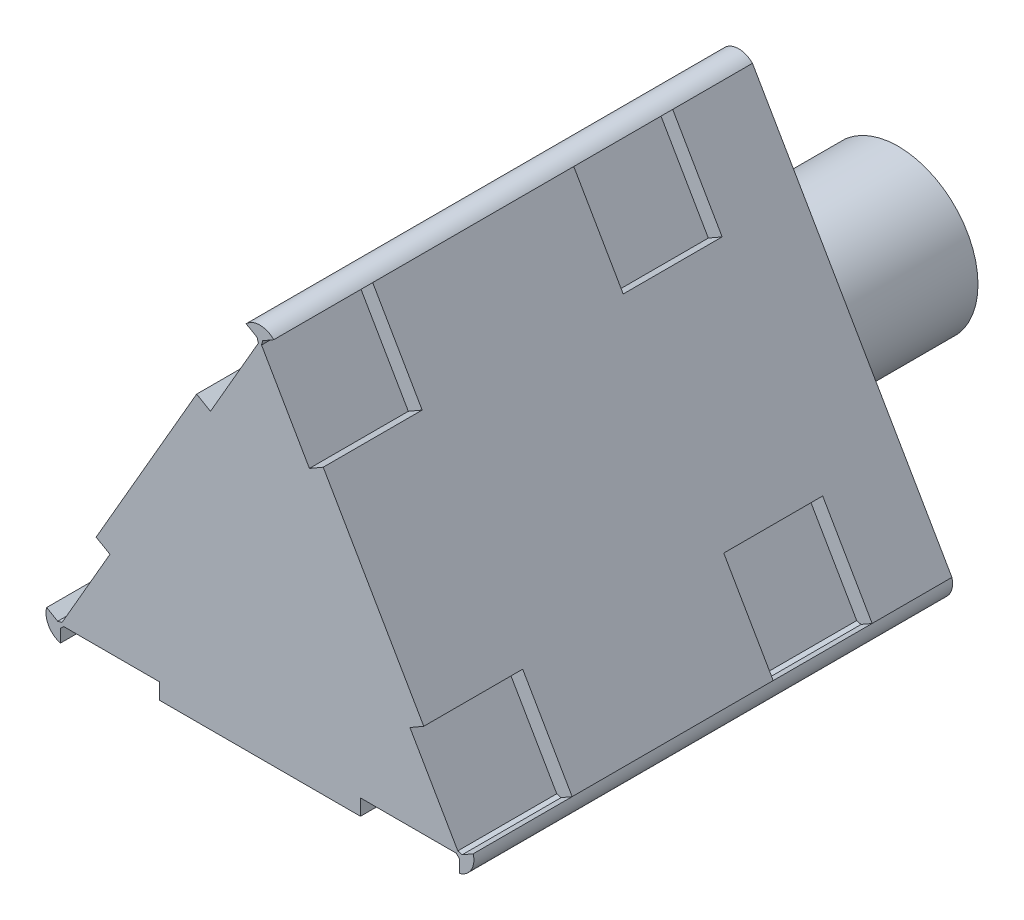
SolidWorks part; units mm, degrees
ref_plane "正面" through (0, 0, 0) normal (0, 0, 1) x (1, 0, 0)
ref_plane "平面" through (0, 0, 0) normal (0, 1, 0) x (1, 0, 0)
ref_plane "右側面" through (0, 0, 0) normal (1, 0, 0) x (0, 0, -1)
sketch "ｽｹｯﾁ1" plane through (0, 0, 0) normal (0, 0, 1) x (1, 0, 0)
  line L0 (0, 21.6506) -> (-12.5, 0)
  line L1 (-12.5, 0) -> (12.5, 0)
  line L2 (12.5, 0) -> (0, 21.6506)
  dimension "D1" = 25
extrude "ﾎﾞｽ - 押し出し1" add sketch "ｽｹｯﾁ1" along normal blind 30
sketch "ｽｹｯﾁ2" plane through (-9.375, 5.4127, 0) normal (-0.866, 0.5, 0) x (0, 0, 1)
  line L0 (30, -6.25) -> (0, -6.25) construction
  line L1 (30, -6.25) -> (23.8, -6.25)
  line L2 (30, -6.25) -> (30, -0.05)
  line L3 (30, -0.05) -> (23.8, -0.05)
  line L4 (23.8, -6.25) -> (23.8, -0.05)
  line L5 (30, 18.75) -> (23.8, 18.75)
  line L6 (30, 18.75) -> (30, 12.55)
  line L7 (30, 12.55) -> (23.8, 12.55)
  line L8 (23.8, 18.75) -> (23.8, 12.55)
  line L9 (11.2, -6.25) -> (5, -6.25)
  line L10 (11.2, -6.25) -> (11.2, -0.05)
  line L11 (11.2, -0.05) -> (5, -0.05)
  line L12 (5, -6.25) -> (5, -0.05)
  line L13 (30, 18.75) -> (0, 18.75) construction
  line L14 (11.2, 18.75) -> (5, 18.75)
  line L15 (11.2, 18.75) -> (11.2, 12.55)
  line L16 (11.2, 12.55) -> (5, 12.55)
  line L17 (5, 18.75) -> (5, 12.55)
  dimension "D1" = 6.2
  dimension "D2" = 6.2
  dimension "D3" = 6.2
  dimension "D4" = 6.2
  dimension "D5" = 6.2
  dimension "D6" = 6.2
  dimension "D7" = 6.2
  dimension "D8" = 6.2
  dimension "D9" = 25
sketch "ｽｹｯﾁ15" plane through (0, 0, 0) normal (0, -1, 0) x (1, 0, 0)
  line L0 (12.5, 30) -> (12.5, 0) construction
  line L1 (-12.5, 30) -> (-6.3, 30)
  line L2 (-12.5, 30) -> (-12.5, 23.8)
  line L3 (-12.5, 23.8) -> (-6.3, 23.8)
  line L4 (-6.3, 30) -> (-6.3, 23.8)
  line L5 (12.5, 30) -> (6.3, 30)
  line L6 (12.5, 30) -> (12.5, 23.8)
  line L7 (12.5, 23.8) -> (6.3, 23.8)
  line L8 (6.3, 30) -> (6.3, 23.8)
  line L9 (12.5, 5) -> (6.3, 5)
  line L10 (12.5, 5) -> (12.5, 11.2)
  line L11 (12.5, 11.2) -> (6.3, 11.2)
  line L12 (6.3, 5) -> (6.3, 11.2)
  line L13 (-12.5, 30) -> (-12.5, 0) construction
  line L14 (-12.5, 5) -> (-6.3, 5)
  line L15 (-12.5, 5) -> (-12.5, 11.2)
  line L16 (-12.5, 11.2) -> (-6.3, 11.2)
  line L17 (-6.3, 5) -> (-6.3, 11.2)
  dimension "D1" = 6.2
  dimension "D2" = 6.2
  dimension "D3" = 6.2
  dimension "D4" = 6.2
  dimension "D5" = 6.2
  dimension "D6" = 6.2
  dimension "D7" = 6.2
  dimension "D8" = 6.2
  dimension "D9" = 25
sketch "ｽｹｯﾁ20" plane through (9.375, 5.4127, 0) normal (0.866, 0.5, 0) x (0, 0, -1)
  line L0 (-30, -6.25) -> (0, -6.25) construction
  line L1 (-30, -6.25) -> (-23.8, -6.25)
  line L2 (-30, -6.25) -> (-30, -0.05)
  line L3 (-30, -0.05) -> (-23.8, -0.05)
  line L4 (-23.8, -6.25) -> (-23.8, -0.05)
  line L5 (-30, 18.75) -> (-23.8, 18.75)
  line L6 (-30, 18.75) -> (-30, 12.55)
  line L7 (-30, 12.55) -> (-23.8, 12.55)
  line L8 (-23.8, 18.75) -> (-23.8, 12.55)
  line L9 (-5, -6.25) -> (-11.2, -6.25)
  line L10 (-5, -6.25) -> (-5, -0.05)
  line L11 (-5, -0.05) -> (-11.2, -0.05)
  line L12 (-11.2, -6.25) -> (-11.2, -0.05)
  line L13 (-30, 18.75) -> (0, 18.75) construction
  line L14 (-5, 18.75) -> (-11.2, 18.75)
  line L15 (-5, 18.75) -> (-5, 12.55)
  line L16 (-5, 12.55) -> (-11.2, 12.55)
  line L17 (-11.2, 18.75) -> (-11.2, 12.55)
  dimension "D1" = 6.2
  dimension "D2" = 6.2
  dimension "D3" = 6.2
  dimension "D4" = 6.2
  dimension "D5" = 6.2
  dimension "D6" = 6.2
  dimension "D7" = 6.2
  dimension "D8" = 6.2
  dimension "D9" = 25
sketch "ｽｹｯﾁ11" plane through (0, 0, 0) normal (0, 0, -1) x (-1, 0, 0)
  line L0 (0, 21.6506) -> (12.5, 0)
  line L1 (0, 21.6506) -> (0.866, 22.1506) construction
  line L2 (-0.866, 22.1506) -> (0, 21.6506) construction
  line L3 (0.866, 22.1506) -> (13.366, 0.5)
  line L4 (12.5, 0) -> (-12.5, 0)
  line L5 (-13.366, 0.5) -> (-12.5, 0) construction
  line L6 (-12.5, 0) -> (-12.5, -1) construction
  line L7 (12.5, -1) -> (-12.5, -1)
  line L8 (0, 21.6506) -> (-12.5, 0)
  line L9 (12.5, 0) -> (12.5, -1) construction
  line L10 (12.5, 0) -> (13.366, 0.5) construction
  line L11 (-0.866, 22.1506) -> (-13.366, 0.5)
  arc A0 (-0.866, 22.1506) -> (0.866, 22.1506) centre (0, 21.2846) cw
  arc A1 (13.366, 0.5) -> (12.5, -1) centre (12.183, 0.183) cw
  arc A2 (-12.5, -1) -> (-13.366, 0.5) centre (-12.183, 0.183) cw
  dimension "D1" = 25
  dimension "D2" = 1
  dimension "D3" = 25
  dimension "D4" = 1
  dimension "D5" = 25
  dimension "D6" = 1
extrude "ﾎﾞｽ - 押し出し8" add sketch "ｽｹｯﾁ11" against normal through all
extrude "ｶｯﾄ - 押し出し5" cut sketch "ｽｹｯﾁ2" along normal blind 1
sketch "ｽｹｯﾁ16" plane through (0, 0, 23.8) normal (0, 0, 1) x (1, 0, 0)
  line L0 (-12.4, 0.1732) -> (-12.6732, 0.1)
  line L1 (-9.4, 5.3694) -> (-12.5, 0) construction
  line L3 (-12.6732, 0.1) -> (-12.5, 0)
  line L4 (-12.5, 0) -> (-12.4, 0.1732)
  line L7 (-13.366, 0.5) -> (-12.5, 0) construction
  dimension "D1" = 0.2
  dimension "D2" = 0.2
extrude "ﾎﾞｽ - 押し出し9" add sketch "ｽｹｯﾁ16" along normal through all and the other way through all
extrude "ｶｯﾄ - 押し出し10" cut sketch "ｽｹｯﾁ15" along normal blind 1
sketch "ｽｹｯﾁ18" plane through (0, 0, 23.8) normal (0, 0, 1) x (1, 0, 0)
  line L0 (-0.1732, 21.7506) -> (0, 21.6506)
  line L1 (-0.866, 22.1506) -> (0, 21.6506) construction
  line L2 (0, 21.6506) -> (-0.1, 21.4774)
  line L3 (0, 21.6506) -> (-3.1, 16.2813) construction
  line L4 (-0.1, 21.4774) -> (-0.1732, 21.7506)
  dimension "D1" = 0.2
  dimension "D2" = 0.2
extrude "ﾎﾞｽ - 押し出し10" add sketch "ｽｹｯﾁ18" against normal through all and the other way through all
sketch "ｽｹｯﾁ19" plane through (0, 0, 23.8) normal (0, 0, 1) x (1, 0, 0)
  line L0 (12.5, 0) -> (12.3, 0)
  line L1 (6.3, 0) -> (12.5, 0) construction
  line L2 (12.3, 0) -> (12.5, -0.2)
  line L3 (12.5, -1) -> (12.5, 0) construction
  line L4 (12.5, -0.2) -> (12.5, 0)
  dimension "D1" = 0.2
  dimension "D2" = 0.2
extrude "ﾎﾞｽ - 押し出し11" add sketch "ｽｹｯﾁ19" against normal through all and the other way through all
extrude "ｶｯﾄ - 押し出し11" cut sketch "ｽｹｯﾁ20" along normal blind 1
sketch "ｽｹｯﾁ21" plane through (0, 0, 23.8) normal (0, 0, 1) x (1, 0, 0)
  line L0 (0, 21.6506) -> (0.1, 21.4774)
  line L1 (3.1, 16.2813) -> (0, 21.6506) construction
  line L2 (0.1, 21.4774) -> (0.1732, 21.7506)
  line L3 (0.866, 22.1506) -> (0, 21.6506) construction
  line L4 (0.1732, 21.7506) -> (0, 21.6506)
  dimension "D1" = 0.2
  dimension "D2" = 0.2
extrude "ﾎﾞｽ - 押し出し12" add sketch "ｽｹｯﾁ21" along normal through all and the other way through all
sketch "ｽｹｯﾁ23" plane through (0, 0, 23.8) normal (0, 0, 1) x (1, 0, 0)
  line L0 (12.5, 0) -> (12.6732, 0.1)
  line L1 (12.6732, 0.1) -> (12.4, 0.1732)
  line L2 (12.5, 0) -> (9.4, 5.3694) construction
  line L3 (12.4, 0.1732) -> (12.5, 0)
  dimension "D1" = 0.2
  dimension "D2" = 0.2
extrude "ﾎﾞｽ - 押し出し13" add sketch "ｽｹｯﾁ23" along normal through all and the other way through all
sketch "ｽｹｯﾁ24" plane through (0, 0, 23.8) normal (0, 0, 1) x (1, 0, 0)
  line L0 (-12.5, 0) -> (-12.3, 0)
  line L1 (-12.5, 0) -> (-6.3, 0) construction
  line L2 (-12.3, 0) -> (-12.5, -0.2)
  line L3 (-12.5, -1) -> (-12.5, 0) construction
  line L4 (-12.5, -0.2) -> (-12.5, 0)
  dimension "D1" = 0.2
  dimension "D2" = 0.2
extrude "ﾎﾞｽ - 押し出し14" add sketch "ｽｹｯﾁ24" along normal through all and the other way through all
sketch "ｽｹｯﾁ25" plane through (0, 0, 0) normal (0, 0, -1) x (-1, 0, 0)
  line L1 (13.366, 0.5) -> (0.866, 22.1506) construction
  line L2 (0, 7.2169) -> (7.116, 11.3253) construction
  line L3 (0, 7.2169) -> (-7.116, 11.3253) construction
  line L4 (-0.866, 22.1506) -> (-13.366, 0.5) construction
  line L5 (0, 7.2169) -> (0, -1) construction
  line L6 (-12.5, -1) -> (12.5, -1) construction
  circle A0 centre (0, 7.2169) radius 5
  dimension "D1" = 10
extrude "ﾎﾞｽ - 押し出し15" add sketch "ｽｹｯﾁ25" along normal blind 10
